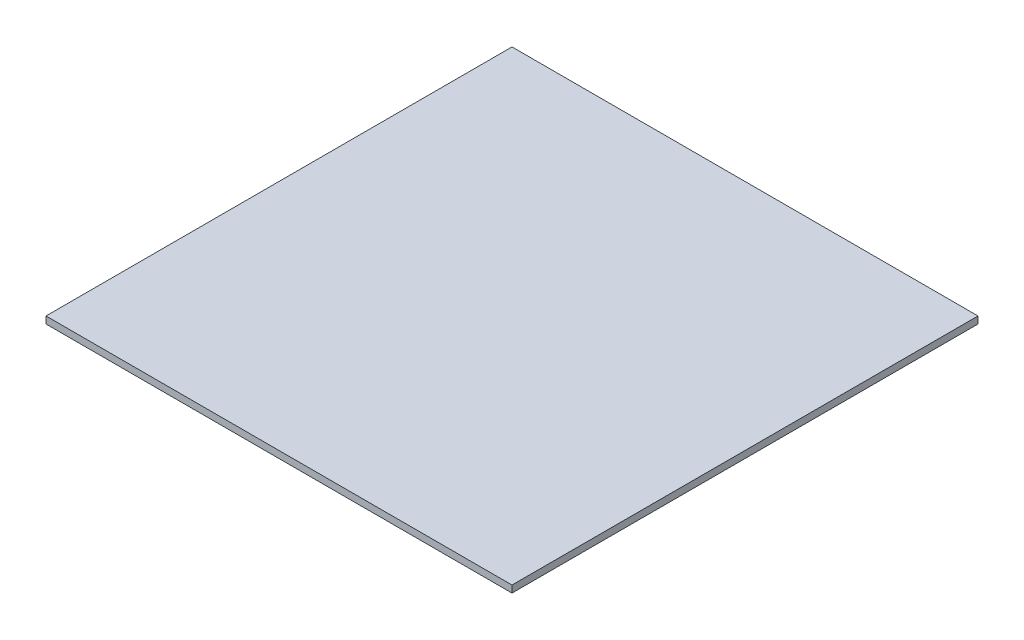
SolidWorks part; units mm, degrees
ref_plane "정면" through (0, 0, 0) normal (0, 0, 1) x (1, 0, 0)
ref_plane "윗면" through (0, 0, 0) normal (0, 1, 0) x (1, 0, 0)
ref_plane "우측면" through (0, 0, 0) normal (1, 0, 0) x (0, 0, -1)
sketch "스케치1" plane through (0, 0, 0) normal (0, 1, 0) x (1, 0, 0)
  line L1 (-100, 100) -> (100, 100)
  line L2 (-100, 100) -> (-100, -100)
  line L3 (-100, -100) -> (100, -100)
  line L4 (100, 100) -> (100, -100)
  line L5 (-100, 100) -> (100, -100) construction
  line L6 (-100, -100) -> (100, 100) construction
  point P0 (0, 0)
  dimension "D1" = 200
  dimension "D2" = 200
extrude "보스-돌출1" add sketch "스케치1" along normal blind 3
